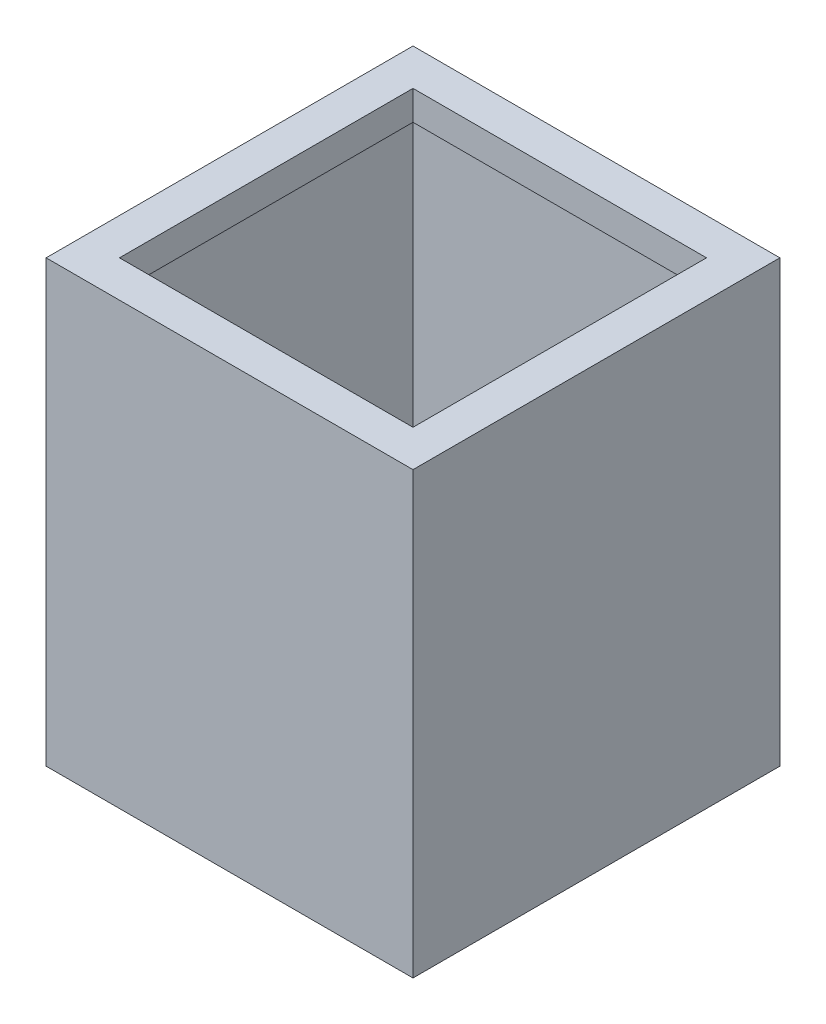
SolidWorks part; units mm, degrees
other "Element opisowy7"
other "Folder spoin"
other "Ścieg spoiny7"
ref_plane "Płaszczyzna przednia" through (0, 0, 0) normal (0, 0, 1) x (1, 0, 0)
ref_plane "Płaszczyzna górna" through (0, 0, 0) normal (0, 1, 0) x (1, 0, 0)
ref_plane "Płaszczyzna prawa" through (0, 0, 0) normal (1, 0, 0) x (0, 0, -1)
sketch "Szkic1" plane through (0, 0, 0) normal (0, 1, 0) x (1, 0, 0)
  line L1 (-159.375, 39.0625) -> (90.625, 39.0625)
  line L2 (-159.375, 39.0625) -> (-159.375, -210.9375)
  line L3 (-159.375, -210.9375) -> (90.625, -210.9375)
  line L4 (90.625, 39.0625) -> (90.625, -210.9375)
  dimension "D1" = 250
  dimension "D2" = 250
extrude "Dodanie-wyciągnięcie1" add sketch "Szkic1" along normal blind 300
sketch "Szkic2" plane through (0, 300, 0) normal (0, 1, 0) x (1, 0, 0)
  line L0 (90.625, 39.0625) -> (-159.375, 39.0625) construction
  line L1 (-154.375, 34.0625) -> (85.625, 34.0625)
  line L2 (-154.375, 34.0625) -> (-154.375, -205.9375)
  line L3 (-154.375, -205.9375) -> (85.625, -205.9375)
  line L4 (85.625, 34.0625) -> (85.625, -205.9375)
  line L5 (-159.375, 39.0625) -> (-159.375, -210.9375) construction
  line L6 (-159.375, -210.9375) -> (90.625, -210.9375) construction
  line L7 (90.625, -210.9375) -> (90.625, 39.0625) construction
  dimension "D1" = 5
  dimension "D2" = 5
  dimension "D3" = 5
  dimension "D4" = 5
extrude "Wytnij-wyciągnięcie1" cut sketch "Szkic2" against normal blind 295
sketch "Szkic3" plane through (0, 300, 0) normal (0, 1, 0) x (1, 0, 0)
  line L0 (-134.375, 14.0625) -> (-134.375, -185.9375)
  line L1 (-154.375, 34.0625) -> (85.625, 34.0625)
  line L2 (-154.375, 34.0625) -> (-154.375, -205.9375)
  line L3 (-154.375, -205.9375) -> (85.625, -205.9375)
  line L4 (85.625, 34.0625) -> (85.625, -205.9375)
  line L5 (-134.375, -185.9375) -> (65.625, -185.9375)
  line L6 (65.625, 14.0625) -> (65.625, -185.9375)
  line L7 (-134.375, 14.0625) -> (65.625, 14.0625)
  dimension "D1" = 20
extrude "Dodanie-wyciągnięcie2" add sketch "Szkic3" against normal blind 20
